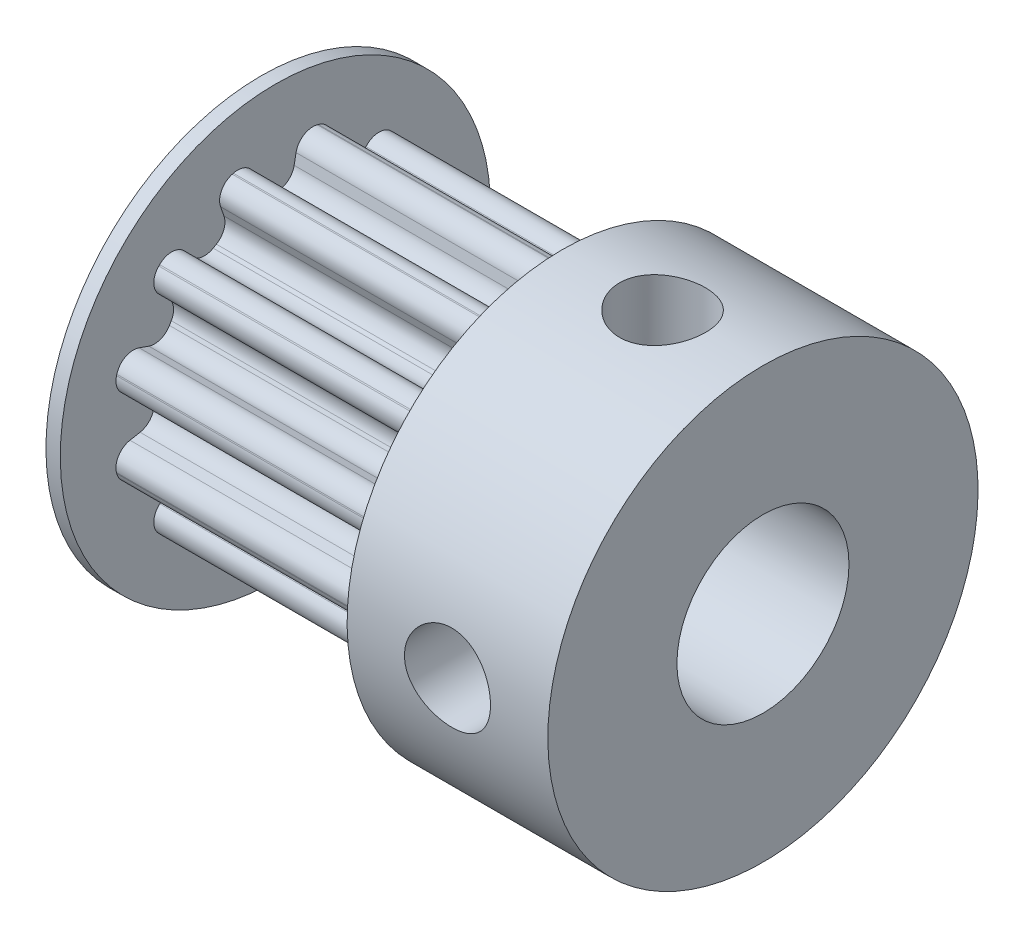
SolidWorks part; units mm, degrees
ref_plane "Ön Düzlem" through (0, 0, 0) normal (0, 0, 1) x (1, 0, 0)
ref_plane "Üst Düzlem" through (0, 0, 0) normal (0, 1, 0) x (1, 0, 0)
ref_plane "Sağ Düzlem" through (0, 0, 0) normal (1, 0, 0) x (0, 0, -1)
sketch "Sketch2" plane through (0, 0, 0) normal (0, 0, 1) x (1, 0, 0)
  line L0 (0, 0) -> (0, 7.5)
  line L1 (0, 7.5) -> (0.5, 7.5)
  line L2 (0.5, 7.5) -> (0.5, 5.73)
  line L3 (0.5, 5.73) -> (10.5, 5.73)
  line L4 (10.5, 5.73) -> (10.5, 7.5)
  line L5 (10.5, 7.5) -> (17.5, 7.5)
  line L8 (17.5, 7.5) -> (17.5, 0)
  line L9 (17.5, 0) -> (0, 0)
  line L12 (19.2122, 0) -> (-1.5493, 0) construction
  point P3 (0, 0)
  point P12 (17.5, 7.5)
  point P14 (0, 0)
  point P15 (17.5, 7.3668)
  dimension "D1" = 7.5
  dimension "D2" = 17.5
  dimension "D3" = 0.5
  dimension "D4" = 10
  dimension "D5" = 5.73
revolve "Revolve1" add sketch "Sketch2" angle 360 about L12
sketch "Sketch3" plane through (0, 0, 0) normal (-1, 0, 0) x (0, 0, 1)
  circle A0 centre (0, 0) radius 3
  dimension "D1" = 6
extrude "Cut-Extrude1" cut sketch "Sketch3" against normal through all
sketch "Sketch5" plane through (0, 0, 0) normal (0, 1, 0) x (1, 0, 0)
  line L0 (10.5, 0) -> (17.5, 0) construction
  line L1 (10.5, 5.73) -> (10.5, -5.73) construction
  line L2 (17.5, -7.5) -> (17.5, 7.5) construction
  circle A0 centre (14, 0) radius 1.5
  dimension "D1" = 3
extrude "Cut-Extrude3" cut sketch "Sketch5" along normal blind 10
pattern_circular "CirPattern1" count 2 over 90 about axis through (19.2122, 0, 0) along (1, 0, 0) of "Cut-Extrude3"
sketch "Sketch4" plane through (0.5, 0, 0) normal (1, 0, 0) x (0, 0, -1)
  line L0 (1.125, 7.23) -> (-1.125, 7.23)
  line L1 (-1.125, 7.23) -> (-0.5625, 4.23)
  line L2 (-0.5625, 4.23) -> (0.5625, 4.23)
  line L3 (0.5625, 4.23) -> (1.125, 7.23)
  circle A0 centre (0, 0) radius 5.73 construction
  point P2 (0, 4.23)
  point P5 (0, 5.73)
  point P7 (0, 0)
  dimension "D1" = 1.125
  dimension "D2" = 2.25
  dimension "D3" = 3
  dimension "D4" = 1.5
extrude "Cut-Extrude2" cut sketch "Sketch4" along normal blind 10
fillet "Fillet1" radius 0.6 4 edges at (5.5, 5.6692, -0.8324) (5.5, 5.6692, 0.8324) (5.5, 4.23, 0.5625) (5.5, 4.23, -0.5625)
pattern_circular "CirPattern2" count 12 over 360 about axis through (0, 0, 0) along (1, 0, 0) of "Fillet1", "Cut-Extrude2"
